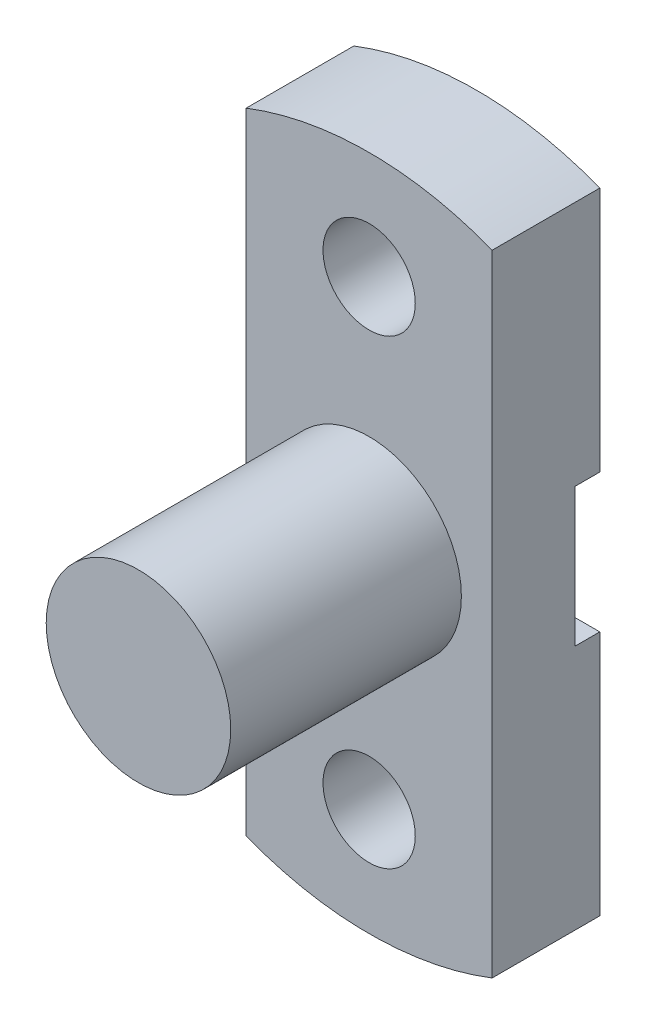
SolidWorks part; units mm, degrees
ref_plane "Front Plane" through (0, 0, 0) normal (0, 0, 1) x (1, 0, 0)
ref_plane "Top Plane" through (0, 0, 0) normal (0, 1, 0) x (1, 0, 0)
ref_plane "Right Plane" through (0, 0, 0) normal (1, 0, 0) x (0, 0, -1)
sketch "Sketch1" plane through (0, 0, 0) normal (0, 0, 1) x (1, 0, 0)
  line L2 (-236.9263, 264.0502) -> (-236.9263, 59.1112)
  line L3 (-156.9263, 264.0502) -> (-156.9263, 59.1112)
  arc A0 (-236.9263, 59.1112) -> (-156.9263, 59.1112) centre (-196.9263, 161.5807) ccw
  circle A1 centre (-196.9263, 236.5807) radius 15
  circle A2 centre (-196.9263, 86.5807) radius 15
  arc A3 (-156.9263, 264.0502) -> (-236.9263, 264.0502) centre (-196.9263, 161.5807) ccw
  point P13 (-236.9263, 161.5807)
  point P16 (-156.9263, 161.5807)
extrude "Boss-Extrude1" add sketch "Sketch1" along normal blind 35
sketch "Sketch2" plane through (0, 0, 35) normal (0, 0, 1) x (1, 0, 0)
  circle A0 centre (-196.9263, 161.5807) radius 30
  dimension "D1" = 60
extrude "Boss-Extrude2" add sketch "Sketch2" along normal blind 75
sketch "Sketch6" plane through (-236.9263, 0, 0) normal (-1, 0, 0) x (0, 0, 1)
  line L0 (0, 264.0502) -> (0, 59.1112) construction
  line L1 (-8, 184.0807) -> (8, 184.0807)
  line L2 (-8, 184.0807) -> (-8, 139.0807)
  line L3 (-8, 139.0807) -> (8, 139.0807)
  line L4 (8, 184.0807) -> (8, 139.0807)
  line L5 (-8, 184.0807) -> (8, 139.0807) construction
  line L6 (-8, 139.0807) -> (8, 184.0807) construction
  point P0 (0, 161.5807)
  dimension "D1" = 45
  dimension "D2" = 16
extrude "Cut-Extrude2" cut sketch "Sketch6" against normal blind 350
